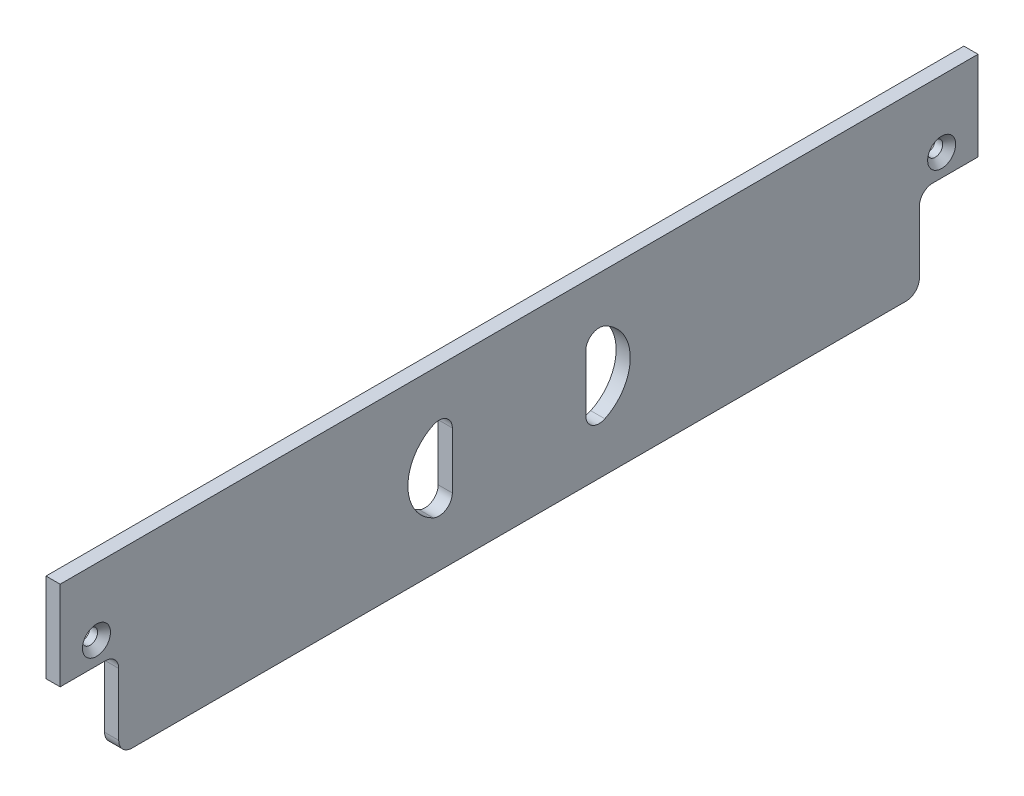
SolidWorks part; units mm, degrees
material "Garolite (G-10/FR4)"
ref_plane "Front Plane" through (0, 0, 0) normal (0, 0, 1) x (1, 0, 0)
ref_plane "Top Plane" through (0, 0, 0) normal (0, 1, 0) x (1, 0, 0)
ref_plane "Right Plane" through (0, 0, 0) normal (1, 0, 0) x (0, 0, -1)
sketch "Sketch1" plane through (0, 0, 0) normal (1, 0, 0) x (0, 0, -1)
  line L0 (-103.175, 20) -> (-103.175, 40)
  line L1 (-103.175, 40) -> (103.175, 40)
  line L2 (0, 0) -> (0, 40) construction
  line L3 (-103.175, 20) -> (-93, 20)
  line L4 (103.175, 20) -> (103.175, 40)
  line L5 (103.175, 20) -> (93, 20)
  line L6 (90, 3) -> (90, 17)
  line L8 (-90, 3) -> (-90, 17)
  line L11 (-87, 0) -> (87, 0)
  arc A0 (-93, 20) -> (-90, 17) centre (-93, 17) cw
  arc A1 (-87, 0) -> (-90, 3) centre (-87, 3) cw
  arc A2 (93, 20) -> (90, 17) centre (93, 17) ccw
  arc A3 (87, 0) -> (90, 3) centre (87, 3) ccw
  dimension "D7" = 3
  dimension "D1" = 40
  dimension "D2" = 206.35
  dimension "D3" = 13.175
  dimension "D4" = 20
extrude "Boss-Extrude1" add sketch "Sketch1" along normal blind 3.175
hole_wizard "CSK for M3 Flat Head Machine Screw1" positions "Sketch3" profile "Sketch2" countersink size "M3" standard "Ansi Metric" end condition through all
sketch "Sketch3" plane through (3.175, 0, 0) normal (1, 0, 0) x (0, 0, -1)
  line L15 (-103.175, 20) -> (-93, 20) construction
  line L16 (-103.175, 40) -> (-103.175, 20) construction
  point P1 (-95, 25)
  dimension "D1" = 5
  dimension "D2" = 8.175
sketch "Sketch2" plane through (3.175, 25, 95) normal (0, 1, 0) x (0, 0, -1)
  line L0 (0, 0) -> (0, 3.175)
  line L1 (0, 3.175) -> (1.7, 3.175)
  line L2 (1.7, 3.175) -> (1.7, 1.45)
  line L3 (1.7, 1.45) -> (3.15, 0)
  line L5 (3.15, 0) -> (0, 0)
  line L6 (-1.7, 1.45) -> (-3.15, 0) construction
  line L11 (0, -6.35) -> (0, 107.95) construction
  dimension "Thru Hole Dia." = 3.4
  dimension "Thru Hole Depth" = 3.175
  dimension "Near C'Sink Dia." = 6.3
  dimension "Near C'Sink Angle" = 90
mirror "Mirror1" about plane through (0, 0, 0) normal (0, 0, 1) of "CSK for M3 Flat Head Machine Screw1"
sketch "Sketch4" plane through (3.175, 0, 0) normal (1, 0, 0) x (0, 0, -1)
  line L0 (-15, 30) -> (-15, 10)
  line L1 (103.175, 40) -> (-103.175, 40) construction
  arc A0 (-15, 30) -> (-15, 10) centre (-15, 20) ccw
  dimension "D1" = 20
  dimension "D2" = 10
  dimension "D3" = 15
extrude "Cut-Extrude1" cut sketch "Sketch4" against normal through all
fillet "Fillet1" radius 3 2 edges at (1.5875, 10, 15) (1.5875, 30, 15)
mirror "Mirror3" about plane through (0, 0, 0) normal (0, 0, 1) of "Cut-Extrude1", "Fillet1"
